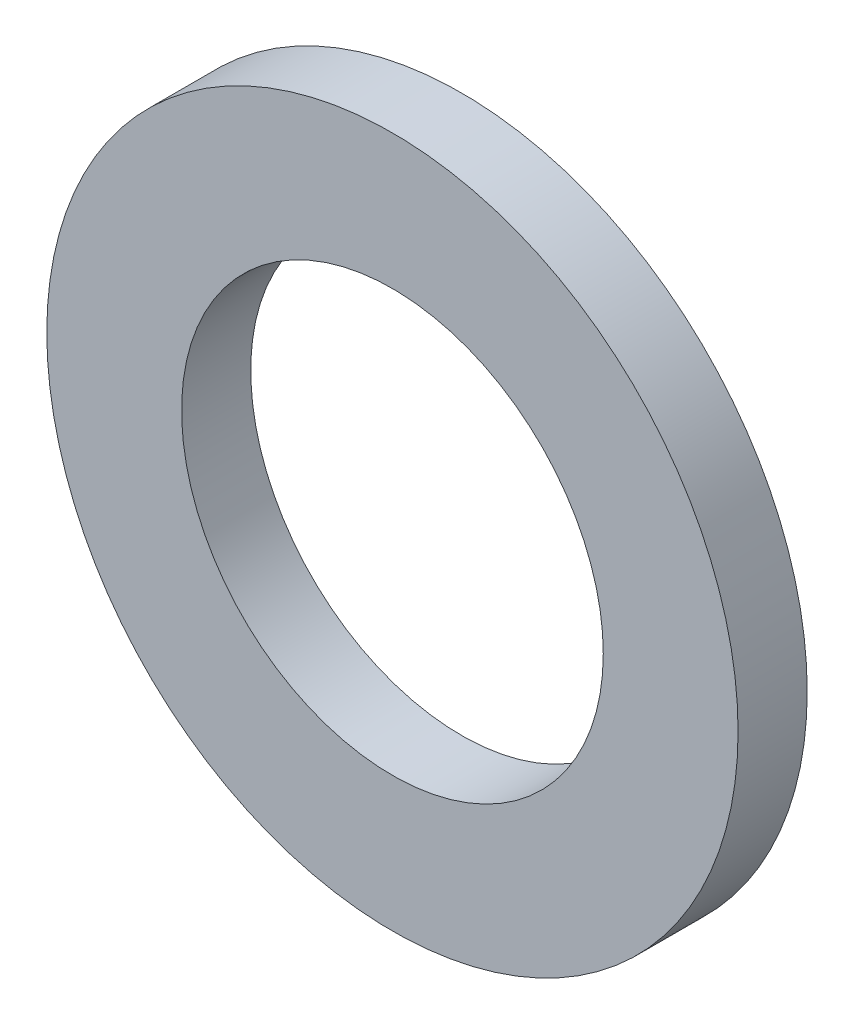
SolidWorks part; units mm, degrees
material "1060-O (SS)"
ref_plane "Ebene vorne" through (0, 0, 0) normal (0, 0, 1) x (1, 0, 0)
ref_plane "Ebene oben" through (0, 0, 0) normal (0, 1, 0) x (1, 0, 0)
ref_plane "Ebene rechts" through (0, 0, 0) normal (1, 0, 0) x (0, 0, -1)
sketch "Sketch1" plane through (0, 0, 0) normal (0, 0, 1) x (1, 0, 0)
  circle A0 centre (0, 0) radius 3.05
  circle A1 centre (0, 0) radius 5
  dimension "D1" = 6.1
  dimension "D2" = 10
extrude "Boss-Extrude1" add sketch "Sketch1" along normal blind 1
